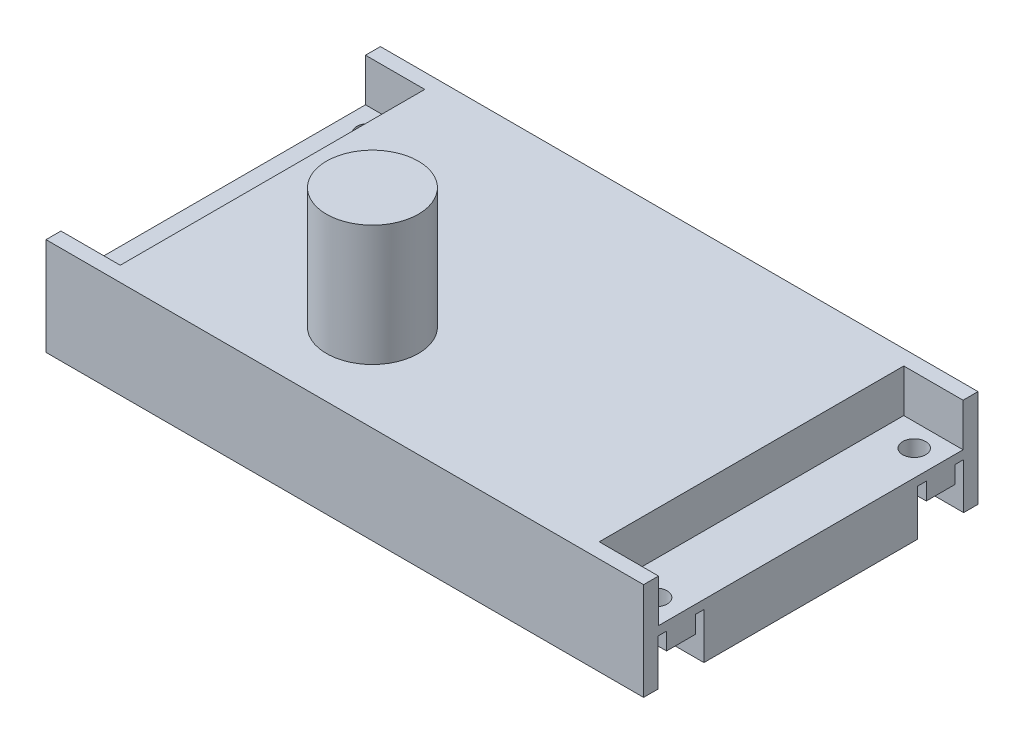
SolidWorks part; units mm, degrees
material "ABS"
ref_plane "Front Plane" through (0, 0, 0) normal (0, 0, 1) x (1, 0, 0)
ref_plane "Top Plane" through (0, 0, 0) normal (0, 1, 0) x (1, 0, 0)
ref_plane "Right Plane" through (0, 0, 0) normal (1, 0, 0) x (0, 0, -1)
sketch "Sketch1" plane through (0, 0, 0) normal (0, 1, 0) x (1, 0, 0)
  line L1 (0, 0) -> (104, 0)
  line L2 (0, 0) -> (0, 58.2)
  line L3 (0, 58.2) -> (104, 58.2)
  line L4 (104, 0) -> (104, 58.2)
  dimension "D1" = 104
  dimension "D2" = 58.2
extrude "Boss-Extrude1" add sketch "Sketch1" along normal blind 17
sketch "Sketch2" plane through (104, 0, 0) normal (1, 0, 0) x (0, 0, -1)
  line L0 (2.5, 0) -> (2.5, 8)
  line L1 (0, 0) -> (58.2, 0) construction
  line L2 (2.5, 8) -> (4, 8)
  line L3 (4, 8) -> (4, 5)
  line L4 (4, 5) -> (9, 5)
  line L5 (9, 5) -> (9, 8)
  line L6 (9, 8) -> (10.5, 8)
  line L7 (10.5, 8) -> (10.5, 0)
  line L8 (0, 17) -> (0, 0) construction
  line L9 (6.5, 5) -> (6.5, 3.7691) construction
  line L10 (10.5, 3.7691) -> (2.5, 3.7691) construction
  line L11 (29.1, 17) -> (29.1, 0) construction
  line L12 (0, 17) -> (58.2, 17) construction
  line L13 (47.7, 8) -> (47.7, 0)
  line L14 (49.2, 8) -> (47.7, 8)
  line L15 (49.2, 5) -> (49.2, 8)
  line L16 (54.2, 5) -> (49.2, 5)
  line L17 (54.2, 8) -> (54.2, 5)
  line L18 (55.7, 8) -> (54.2, 8)
  line L19 (55.7, 0) -> (55.7, 8)
  line L20 (2.5, 0) -> (10.5, 0)
  line L21 (47.7, 0) -> (55.7, 0)
  dimension "D1" = 2.5
  dimension "D2" = 8
  dimension "D3" = 5
  dimension "D4" = 5
  dimension "D5" = 8
extrude "Cut-Extrude2" cut sketch "Sketch2" against normal through all
sketch "Sketch3" plane through (0, 17, 0) normal (0, 1, 0) x (1, 0, 0)
  circle A0 centre (41.5735, 15.2366) radius 8
  dimension "D1" = 16
extrude "Boss-Extrude2" add sketch "Sketch3" along normal blind 21
hole_wizard "Ø4.0mm Dowel Hole1" positions "Sketch4" profile "Sketch5" hole size "Ø4.0" standard "ANSI Metric" end condition through all
sketch "Sketch4" plane through (0, 5, 0) normal (0, -1, 0) x (-1, 0, 0)
  line L0 (0, 0) -> (-104, 0) construction
  line L1 (0, 9) -> (0, 4) construction
  point P0 (-4.5, 51.6)
  point P2 (-4.5, 6.6)
  point P4 (-99.5, 6.6)
  point P6 (-99.5, 51.6)
  dimension "D1" = 45
  dimension "D2" = 95
  dimension "D3" = 6.6
  dimension "D4" = 4.5
sketch "Sketch5" plane through (4.5, 5, -51.6) normal (1, 0, 0) x (0, 0, -1)
  line L0 (0, 0) -> (0, 33)
  line L1 (0, 33) -> (2, 33)
  line L2 (2, 33) -> (2, 0)
  line L5 (2, 0) -> (0, 0)
  line L11 (0, -6.35) -> (0, 107.95) construction
  dimension "Thru Hole Dia." = 4
  dimension "Thru Hole Depth" = 33
sketch "Sketch6" plane through (104, 0, 0) normal (1, 0, 0) x (0, 0, -1)
  line L0 (0, 17) -> (58.2, 17) construction
  line L1 (2.6, 17) -> (55.6, 17)
  line L2 (2.6, 17) -> (2.6, 9.525)
  line L3 (2.6, 9.525) -> (55.6, 9.525)
  line L4 (55.6, 17) -> (55.6, 9.525)
  line L5 (10.5, 0) -> (47.7, 0) construction
  line L6 (29.1, 9.525) -> (29.1, 17) construction
  dimension "D1" = 9.525
  dimension "D2" = 53
extrude "Cut-Extrude3" cut sketch "Sketch6" against normal blind 10.3187
ref_plane "Plane1" through (52, 0, 0) normal (-1, 0, 0) x (0, 0, 1)
mirror "Mirror1" about plane through (52, 0, 0) normal (-1, 0, 0) of "Cut-Extrude3"
